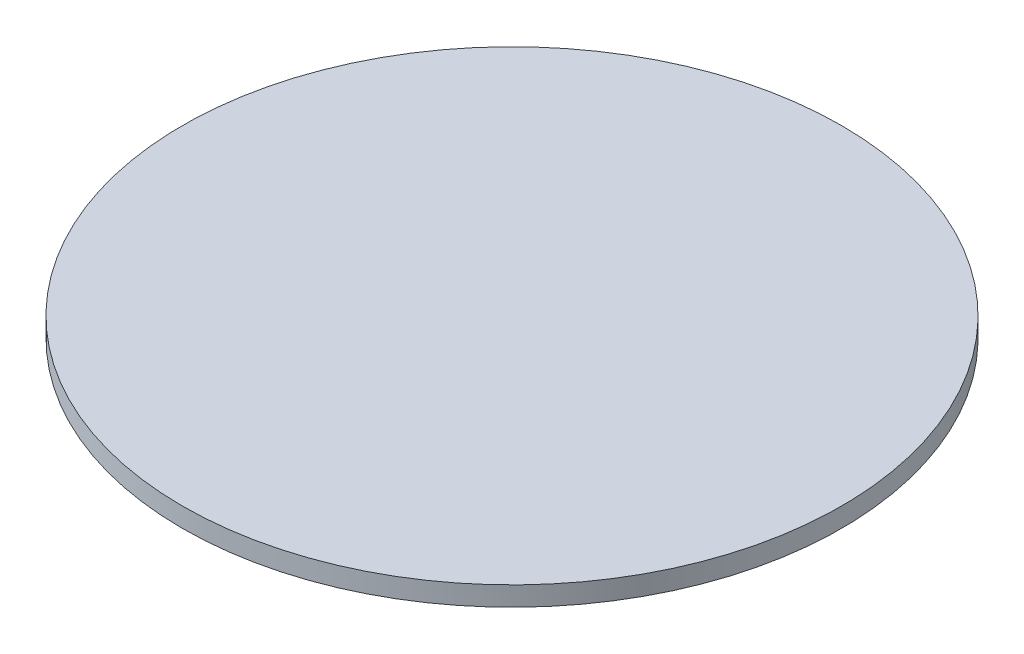
SolidWorks part; units mm, degrees
ref_plane "Front Plane" through (0, 0, 0) normal (0, 0, 1) x (1, 0, 0)
ref_plane "Top Plane" through (0, 0, 0) normal (0, 1, 0) x (1, 0, 0)
ref_plane "Right Plane" through (0, 0, 0) normal (1, 0, 0) x (0, 0, -1)
sketch "Sketch1" plane through (0, 0, 0) normal (0, 1, 0) x (1, 0, 0)
  circle A0 centre (8.8155, 5.8295) radius 51
extrude "Boss-Extrude1" add sketch "Sketch1" along normal blind 3
